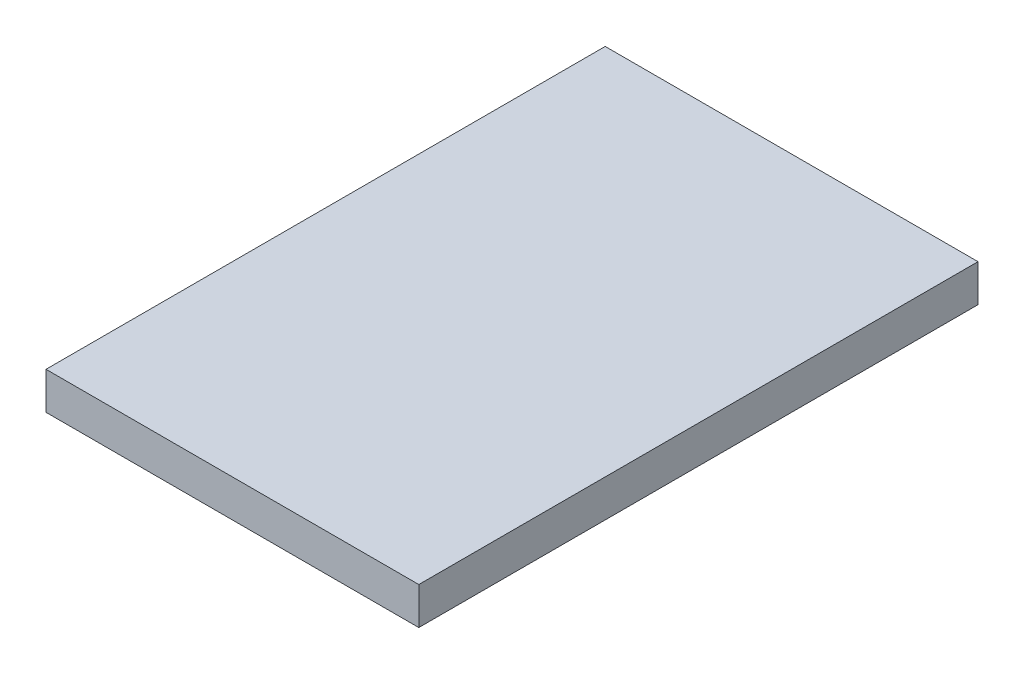
SolidWorks part; units mm, degrees
ref_plane "Front Plane" through (0, 0, 0) normal (0, 0, 1) x (1, 0, 0)
ref_plane "Top Plane" through (0, 0, 0) normal (0, 1, 0) x (1, 0, 0)
ref_plane "Right Plane" through (0, 0, 0) normal (1, 0, 0) x (0, 0, -1)
sketch "Sketch2" plane through (0, 0, 0) normal (0, 1, 0) x (1, 0, 0)
  line L1 (5, -7.5) -> (-5, -7.5)
  line L2 (5, -7.5) -> (5, 7.5)
  line L3 (5, 7.5) -> (-5, 7.5)
  line L4 (-5, -7.5) -> (-5, 7.5)
  line L5 (5, -7.5) -> (-5, 7.5) construction
  line L6 (5, 7.5) -> (-5, -7.5) construction
  point P0 (0, 0)
  dimension "D1" = 10
  dimension "D2" = 15
extrude "Boss-Extrude1" add sketch "Sketch2" along normal blind 1
